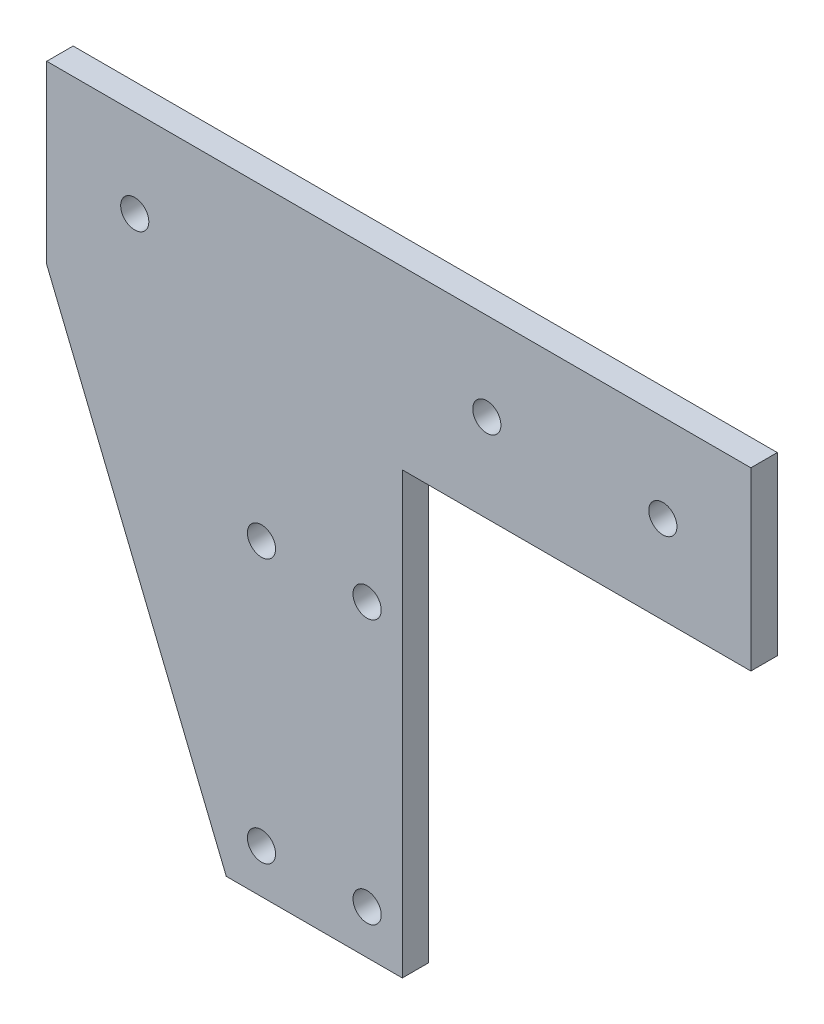
SolidWorks part; units mm, degrees
material "Thornel Mat VMA"
ref_plane "Front Plane" through (0, 0, 0) normal (0, 0, 1) x (1, 0, 0)
ref_plane "Top Plane" through (0, 0, 0) normal (0, 1, 0) x (1, 0, 0)
ref_plane "Right Plane" through (0, 0, 0) normal (1, 0, 0) x (0, 0, -1)
sketch "Sketch1" plane through (0, 0, 0) normal (0, 0, 1) x (1, 0, 0)
  line L0 (-182.8582, 20) -> (-182.8582, 0)
  line L1 (-234.4582, 20) -> (284.7418, 20) construction
  line L3 (-182.8582, 0) -> (-162.4582, -50)
  line L4 (-152.8582, -480) -> (-152.8582, 0) construction
  line L5 (-162.4582, -50) -> (-142.4582, -50)
  line L6 (-132.8582, -480) -> (-132.8582, 0) construction
  line L8 (-132.8582, 0) -> (183.1418, 0) construction
  line L9 (-102.8582, 0) -> (-102.8582, 20)
  line L10 (-102.8582, 20) -> (-182.8582, 20)
  line L13 (-111.1425, 0) -> (-142.4582, 0)
  line L14 (-182.8582, 10) -> (-102.8582, 10) construction
  line L15 (-152.4582, -50) -> (-152.4582, 20) construction
  line L16 (-111.1425, 0) -> (-102.8582, 0)
  line L17 (-158.4582, -15) -> (-146.4582, -15) construction
  line L18 (-158.4582, -15) -> (-158.4582, -45) construction
  line L19 (-158.4582, -45) -> (-146.4582, -45) construction
  line L20 (-146.4582, -15) -> (-146.4582, -45) construction
  line L21 (-142.4582, 0) -> (-142.4582, -50)
  line L24 (-142.4582, -470) -> (-142.4582, 0) construction
  circle A0 centre (-172.8582, 10) radius 1.6
  circle A1 centre (-112.8582, 10) radius 1.6
  circle A2 centre (-132.8582, 10) radius 1.6
  circle A4 centre (-158.4582, -15) radius 1.6
  circle A5 centre (-146.4582, -15) radius 1.6
  circle A6 centre (-158.4582, -45) radius 1.6
  circle A7 centre (-146.4582, -45) radius 1.6
  point P4 (-177.8582, 0)
  point P5 (-152.8582, -54.3217)
  point P38 (-132.8582, -52.7133)
  point P39 (-177.8582, 0)
  point P42 (-142.4582, -0.2892)
  point P43 (-142.4582, 0)
  point P44 (-132.8582, 0)
  point P45 (-142.7505, 0)
  dimension "D5" = 3.2
  dimension "D6" = 10
  dimension "D7" = 10
  dimension "D8" = 20
  dimension "D2" = 30
  dimension "D3" = 30
  dimension "D4" = 10
  dimension "D9" = 12
  dimension "D10" = 6
  dimension "D11" = 5
  dimension "D12" = 30
  dimension "D13" = 50
extrude "Extrude1" add sketch "Sketch1" along normal blind 3
